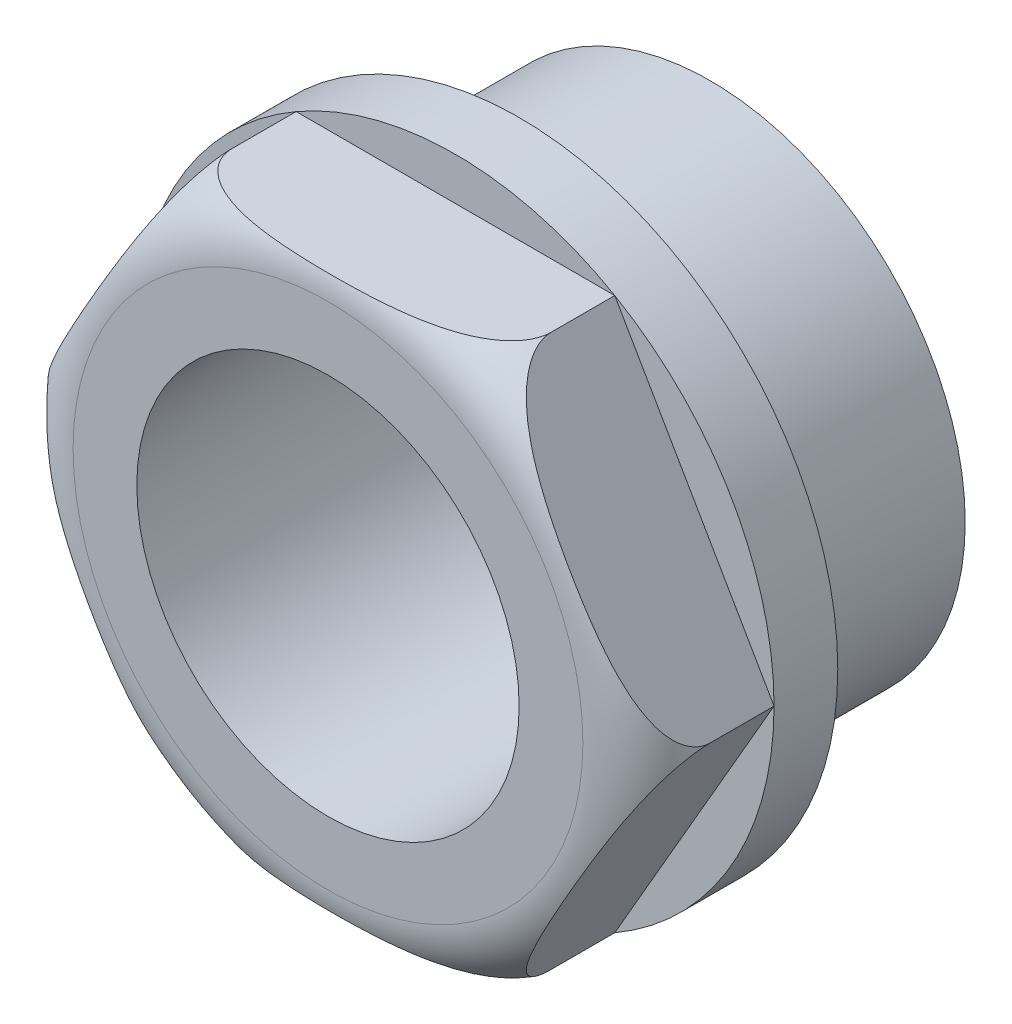
SolidWorks part; units mm, degrees
ref_plane "前视基准面" through (0, 0, 0) normal (0, 0, 1) x (1, 0, 0)
ref_plane "上视基准面" through (0, 0, 0) normal (0, 1, 0) x (1, 0, 0)
ref_plane "右视基准面" through (0, 0, 0) normal (1, 0, 0) x (0, 0, -1)
sketch "草图1" plane through (0, 0, 0) normal (0, 0, 1) x (1, 0, 0)
  circle A0 centre (0, 0) radius 8
  dimension "D1" = 16
extrude "凸台-拉伸1" add sketch "草图1" along normal blind 6
sketch "草图2" plane through (0, 0, 6) normal (0, 0, 1) x (1, 0, 0)
  circle A0 centre (0, 0) radius 10
  dimension "D1" = 20
extrude "凸台-拉伸2" add sketch "草图2" along normal blind 6
fillet "圆角1" radius 2 1 edges at (10, 0, 12)
sketch "草图3" plane through (0, 0, 12) normal (0, 0, 1) x (1, 0, 0)
  line L1 (10, 0) -> (5, 8.6603)
  line L2 (5, 8.6603) -> (-5, 8.6603)
  line L3 (-5, 8.6603) -> (-10, 0)
  line L4 (-10, 0) -> (-5, -8.6603)
  line L5 (-5, -8.6603) -> (5, -8.6603)
  line L6 (5, -8.6603) -> (10, 0)
  circle A0 centre (0, 0) radius 8.6603 construction
extrude "切除-拉伸1" cut sketch "草图3" against normal blind 4 flip side to cut
sketch "草图4" plane through (0, 0, 0) normal (0, 0, -1) x (-1, 0, 0)
  circle A0 centre (0, 0) radius 6
  dimension "D1" = 12
extrude "切除-拉伸2" cut sketch "草图4" against normal blind 12
